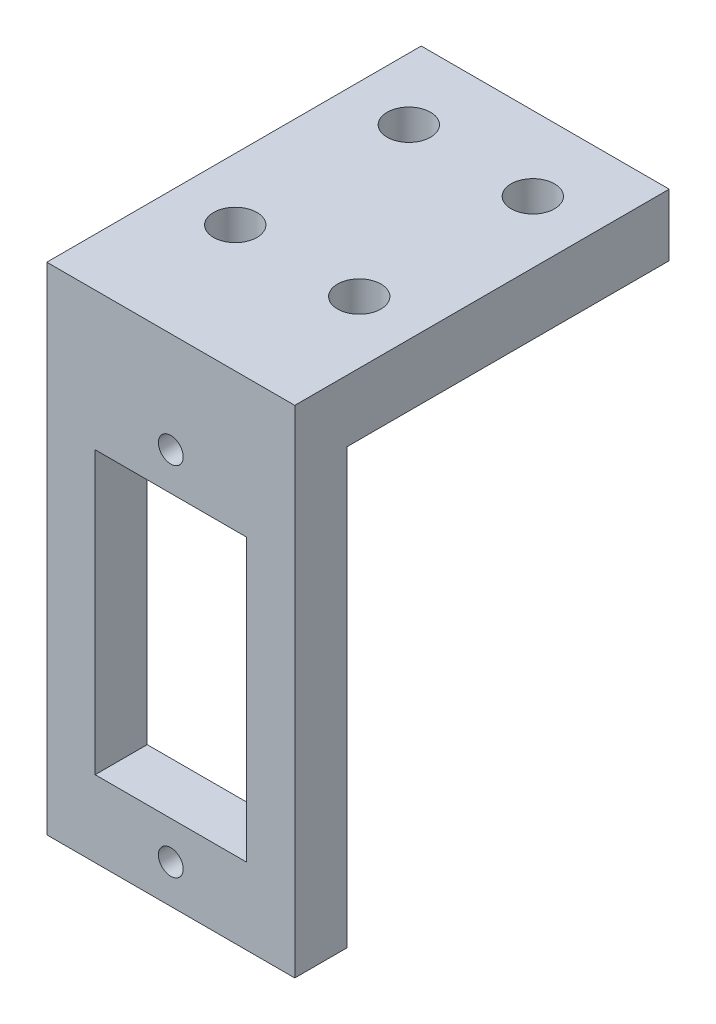
SolidWorks part; units mm, degrees
ref_plane "Front Plane" through (0, 0, 0) normal (0, 0, 1) x (1, 0, 0)
ref_plane "Top Plane" through (0, 0, 0) normal (0, 1, 0) x (1, 0, 0)
ref_plane "Right Plane" through (0, 0, 0) normal (1, 0, 0) x (0, 0, -1)
sketch "Sketch1" plane through (0, 0, 0) normal (0, 0, 1) x (1, 0, 0)
  line L1 (-10, 22.5) -> (10, 22.5)
  line L2 (-10, 22.5) -> (-10, -22.5)
  line L3 (-10, -22.5) -> (10, -22.5)
  line L4 (10, 22.5) -> (10, -22.5)
  line L5 (-10, 22.5) -> (10, -22.5) construction
  line L6 (-10, -22.5) -> (10, 22.5) construction
  point P0 (0, 0)
  dimension "D1" = 20
  dimension "D2" = 45
extrude "Boss-Extrude1" add sketch "Sketch1" along normal blind 4.2
sketch "Sketch2" plane through (0, 0, 0) normal (0, 0, -1) x (-1, 0, 0)
  line L1 (-6.1, 11.35) -> (6.1, 11.35)
  line L2 (-6.1, 11.35) -> (-6.1, -11.35)
  line L3 (-6.1, -11.35) -> (6.1, -11.35)
  line L4 (6.1, 11.35) -> (6.1, -11.35)
  line L5 (-6.1, 11.35) -> (6.1, -11.35) construction
  line L6 (-6.1, -11.35) -> (6.1, 11.35) construction
  point P0 (0, 0)
  dimension "D1" = 12.2
  dimension "D2" = 22.7
extrude "Cut-Extrude1" cut sketch "Sketch2" against normal blind 5
sketch "Sketch3" plane through (0, 0, 4.2) normal (0, 0, 1) x (1, 0, 0)
  line L0 (0, 28.0498) -> (0, 14.4) construction
  line L1 (-23.3516, 0) -> (20.7733, 0) construction
  line L4 (0, 0) -> (0, -11.35) construction
  line L5 (6.1, -11.35) -> (-6.1, -11.35) construction
  line L6 (0, -15.3977) -> (0, -28.1945) construction
  circle A0 centre (0, 14.4) radius 1
  circle A1 centre (0, -14.3964) radius 1.0013
  dimension "D2" = 2
extrude "Cut-Extrude2" cut sketch "Sketch3" against normal blind 5
sketch "Sketch4" plane through (0, 0, 0) normal (0, 0, -1) x (-1, 0, 0)
  line L0 (10, 22.5) -> (10, -22.5) construction
  line L1 (-10, 22.5) -> (10, 22.5)
  line L2 (-10, 22.5) -> (-10, 17.5)
  line L3 (-10, 17.5) -> (10, 17.5)
  line L4 (10, 22.5) -> (10, 17.5)
  dimension "D1" = 5
extrude "Boss-Extrude2" add sketch "Sketch4" along normal blind 26
sketch "Sketch5" plane through (0, 22.5, 0) normal (0, 1, 0) x (1, 0, 0)
  line L0 (-5, 13.2782) -> (-5, -4.3756) construction
  line L1 (-10, 26) -> (10, 26) construction
  line L2 (5, 13.2782) -> (5, -4.7999) construction
  line L3 (-13.9359, 20) -> (16.819, 20) construction
  line L4 (-14.6844, 6) -> (14.3254, 6) construction
  line L6 (-18.6328, 13) -> (14.7823, 13) construction
  circle A0 centre (-5, 6) radius 1.75
  circle A1 centre (5, 6) radius 1.75
  circle A2 centre (5, 20) radius 1.75
  circle A3 centre (-5, 20) radius 1.75
  dimension "D5" = 3.5
  dimension "D6" = 3.5
  dimension "D3" = 6
  dimension "D1" = 10
  dimension "D2" = 20
extrude "Cut-Extrude3" cut sketch "Sketch5" against normal blind 15
sketch "Sketch6" plane through (0, 0, 4.2) normal (0, 0, 1) x (1, 0, 0)
  line L0 (10, -22.5) -> (10, 22.5) construction
  line L1 (-10, -22.5) -> (10, -22.5)
  line L2 (-10, -22.5) -> (-10, -17.5)
  line L3 (-10, -17.5) -> (10, -17.5)
  line L4 (10, -22.5) -> (10, -17.5)
  dimension "D1" = 5
extrude "Cut-Extrude4" cut sketch "Sketch6" against normal blind 15
